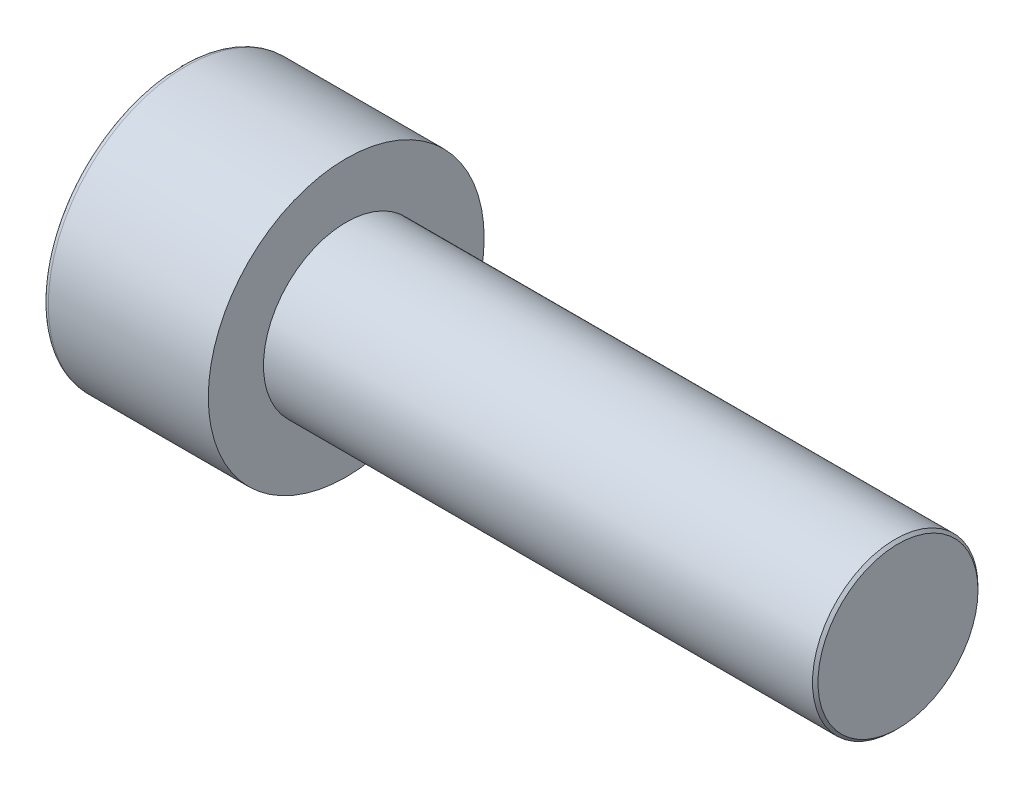
SolidWorks part; units mm, degrees
ref_plane "Front" through (0, 0, 0) normal (0, 0, 1) x (1, 0, 0)
ref_plane "Top" through (0, 0, 0) normal (0, 1, 0) x (1, 0, 0)
ref_plane "Right" through (0, 0, 0) normal (1, 0, 0) x (0, 0, -1)
sketch "Sketch1" plane through (0, 0, 0) normal (1, 0, 0) x (0, 0, -1)
  circle A0 centre (0, 0) radius 5
  dimension "dk" = 10
extrude "BaseHead" add sketch "Sketch1" along normal blind 6
sketch "Sketch2" plane through (6, 0, 0) normal (1, 0, 0) x (0, 0, -1)
  circle A0 centre (0, 0) radius 3
  dimension "d" = 6
extrude "BaseBody" add sketch "Sketch2" along normal blind 20
cosmetic thread "ThreadCosmetic1" [suppressed] parameters "b"=20, "D2"=4.917
sketch "Sketch3" plane through (0, 0, 0) normal (1, 0, 0) x (0, 0, -1)
  line L1 (2.8868, 0) -> (1.4434, 2.5)
  line L2 (1.4434, 2.5) -> (-1.4434, 2.5)
  line L3 (-1.4434, 2.5) -> (-2.8868, 0)
  line L4 (-2.8868, 0) -> (-1.4434, -2.5)
  line L5 (-1.4434, -2.5) -> (1.4434, -2.5)
  line L6 (1.4434, -2.5) -> (2.8868, 0)
  circle A0 centre (0, 0) radius 2.5 construction
  dimension "s" = 5
  dimension "e" = 5.7735
extrude "HexagonSocket" cut sketch "Sketch3" along normal blind 3
sketch "Sketch4" plane through (-4.1961, 0.75, 0) normal (0, 0, 1) x (-1, 0, 0)
  line L0 (-7.1961, 3.25) -> (-8.6395, 0.75)
  line L2 (-8.6395, 0.75) -> (-7.1961, 0.75)
  line L3 (-7.1961, 0.75) -> (-7.1961, 3.25)
  line L4 (-5.0351, 0.75) -> (0.839, 0.75) construction
  line L5 (-30.1961, 0.75) -> (-10.1961, 0.75) construction
  line L6 (-10.1961, 0.75) -> (-4.1961, 0.75) construction
  dimension "m" = 60
revolve "Cut-Revolve1" cut sketch "Sketch4" angle 360 about L4
fillet "HeadFillet" [suppressed] radius 0.25
fillet "TopFillet" radius 0.2 1 edges at (0, 0, -5)
chamfer "Chamfer1" distance 0.1 angle 45 1 edges at (26, 0, -3)
sketch "Sketch5" plane through (0, 0, 0) normal (0, 0, 1) x (1, 0, 0)
  line L0 (25.9, 0.6268) -> (26, 0.8)
  line L1 (26, 0.8) -> (26, 1)
  line L2 (26, 1) -> (25.8, 1)
  line L3 (25.8, 1) -> (25.8, 0.8)
  line L4 (25.8, 0.8) -> (25.9, 0.6268)
  line L5 (0, 0) -> (7.8886, 0) construction
  line L6 (25.9, -3) -> (25.9, 3) construction
  dimension "D1" = 1.6
  dimension "D2" = 0.2
revolve "Cut-Revolve10" [suppressed] cut sketch "Sketch5" angle 360 about L5
pattern_linear "LPattern10" [suppressed] count 12 spacing 0.24 along (1, 0, 0)
equation "\"r1@TopFillet\" = \"d@Sketch2\" / 8"
equation "\"D1@Chamfer1\" = \"r@HeadFillet\""
equation "\"D1@Sketch5\" = \"d@Sketch2\""
equation "\"D2@Sketch5\" =  ( \"d@Sketch2\" - \"D2@ThreadCosmetic1\" )  / 2"
equation "\"D3@LPattern10\" = \"D2@Sketch5\" * 1.2"
equation "\"D1@LPattern10\" = \"b@ThreadCosmetic1\" / \"D3@LPattern10\""
